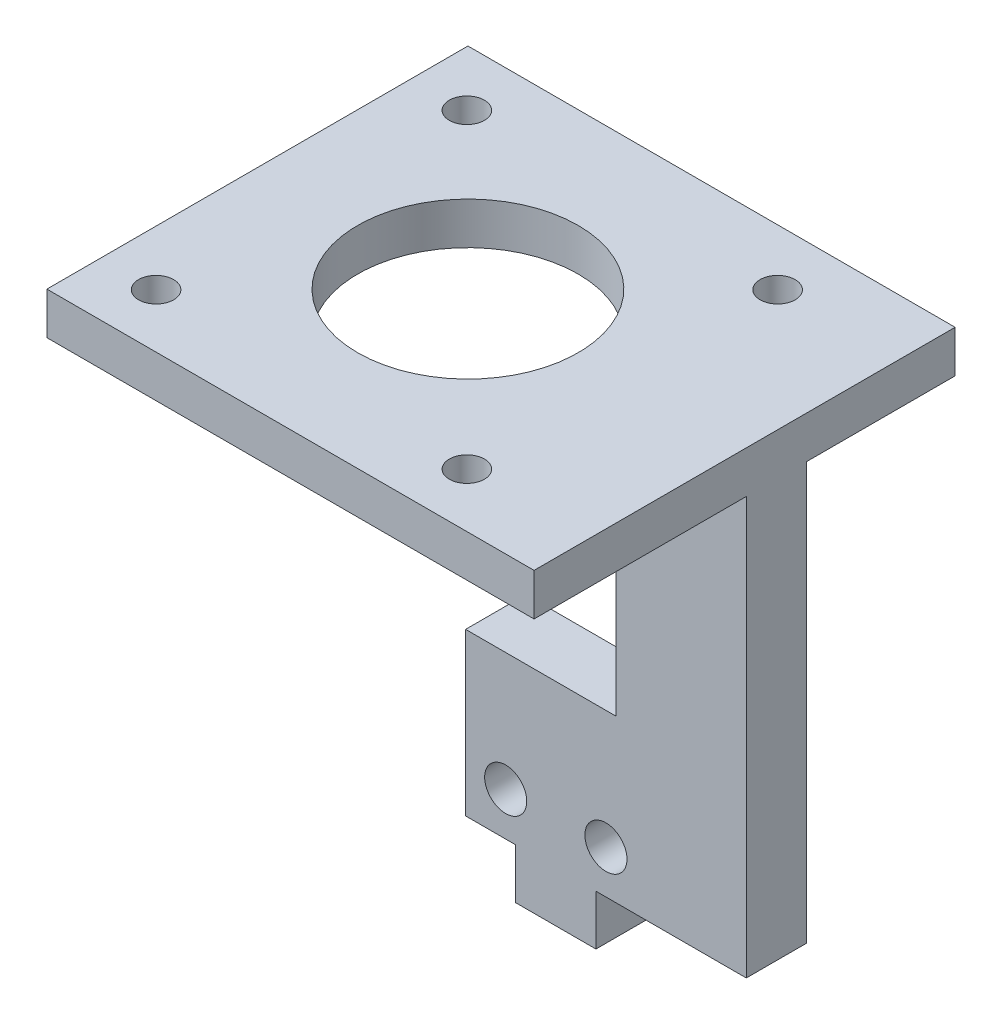
SolidWorks part; units mm, degrees
ref_plane "前视基准面" through (0, 0, 0) normal (0, 0, 1) x (1, 0, 0)
ref_plane "上视基准面" through (0, 0, 0) normal (0, 1, 0) x (1, 0, 0)
ref_plane "右视基准面" through (0, 0, 0) normal (1, 0, 0) x (0, 0, -1)
sketch "草图1" plane through (0, 0, 0) normal (0, 0, 1) x (1, 0, 0)
  line L1 (0, 0) -> (18, 0)
  line L2 (0, 0) -> (0, 50)
  line L3 (0, 50) -> (18, 50)
  line L4 (18, 0) -> (18, 50)
  dimension "D1" = 18
  dimension "D2" = 50
extrude "凸台-拉伸1" add sketch "草图1" along normal blind 6
sketch "草图3" plane through (0, 0, 6) normal (0, 0, 1) x (1, 0, 0)
  line L0 (9, 0) -> (9, 21.4804) construction
  line L1 (0, 0) -> (18, 0) construction
  circle A0 centre (4, 4.3045) radius 2.1
  circle A1 centre (14, 4.3045) radius 2.1
  dimension "D1" = 4.2
  dimension "D2" = 10
  dimension "D3" = 4.3045
extrude "切除-拉伸2" cut sketch "草图3" against normal blind 6
sketch "草图4" plane through (0, 0, 0) normal (0, -1, 0) x (1, 0, 0)
  line L0 (9, 6) -> (9, -13.3054) construction
  line L1 (0, 6) -> (18, 6) construction
  line L3 (13, 6) -> (5, 6)
  line L4 (13, 6) -> (13, -4)
  line L5 (13, -4) -> (5, -4)
  line L6 (5, 6) -> (5, -4)
  dimension "D1" = 8
  dimension "D2" = 10
extrude "凸台-拉伸2" add sketch "草图4" along normal blind 5
sketch "草图5" plane through (18, 0, 0) normal (1, 0, 0) x (0, 0, -1)
  line L0 (-6, 0) -> (-6, 50) construction
  line L1 (0, 0) -> (-6, 0)
  line L2 (0, 0) -> (0, 50)
  line L3 (0, 50) -> (-6, 50)
  line L4 (-6, 0) -> (-6, 50)
  line L5 (-6, 50) -> (0, 50) construction
  dimension "D1" = 0
extrude "凸台-拉伸3" add sketch "草图5" along normal blind 10
sketch "草图6" plane through (0, 0, 6) normal (0, 0, 1) x (1, 0, 0)
  line L0 (0, 50) -> (0, 0) construction
  line L1 (0, 16.1194) -> (15, 16.1194)
  line L2 (0, 16.1194) -> (0, 50)
  line L3 (0, 50) -> (15, 50)
  line L4 (15, 16.1194) -> (15, 50)
  line L5 (28, 50) -> (0, 50) construction
  dimension "D1" = 15
extrude "切除-拉伸3" cut sketch "草图6" against normal blind 10
sketch "草图7" plane through (0, 50, 0) normal (0, 1, 0) x (1, 0, 0)
  line L1 (28, -6) -> (9.8054, -6)
  line L2 (28, -6) -> (28, 2.4383)
  line L3 (28, 2.4383) -> (9.8054, 2.4383)
  line L4 (9.8054, -6) -> (9.8054, 2.4383)
extrude "切除-拉伸4" cut sketch "草图7" against normal blind 4.2
sketch "草图8" plane through (0, 45.8, 0) normal (0, 1, 0) x (1, 0, 0)
  line L0 (15, -6) -> (28, -6) construction
  line L1 (28, -27.17) -> (-30.5473, -27.17)
  line L2 (28, -27.17) -> (28, 14.83)
  line L3 (28, 14.83) -> (-30.5473, 14.83)
  line L4 (-30.5473, -27.17) -> (-30.5473, 14.83)
  line L5 (15, 0) -> (28, 0) construction
  dimension "D1" = 21.17
  dimension "D2" = 14.83
extrude "凸台-拉伸4" add sketch "草图8" against normal blind 4.2
sketch "草图9" plane through (-30.5473, 0, 0) normal (-1, 0, 0) x (0, 0, 1)
  line L1 (27.17, 45.8) -> (-22.0558, 45.8)
  line L2 (27.17, 45.8) -> (27.17, 39.7485)
  line L3 (27.17, 39.7485) -> (-22.0558, 39.7485)
  line L4 (-22.0558, 45.8) -> (-22.0558, 39.7485)
extrude "切除-拉伸5" cut sketch "草图9" against normal blind 9.95
sketch "草图15" plane through (0, 41.6, 0) normal (0, -1, 0) x (1, 0, 0)
  line L0 (0.4024, -12.4657) -> (0.4024, 23.6426) construction
  line L1 (0.4024, 6.2762) -> (-16.0251, 6.2762) construction
  line L2 (28, -14.83) -> (-20.5973, -14.83) construction
  line L3 (28, 0) -> (28, -14.83) construction
  circle A0 centre (15.9024, -9.2238) radius 1.75
  circle A1 centre (-15.0976, -9.2238) radius 1.75
  circle A2 centre (15.9024, 21.7762) radius 1.75
  circle A3 centre (-15.0976, 21.7762) radius 1.75
  dimension "D1" = 3.5
  dimension "D2" = 31
  dimension "D3" = 31
  dimension "D4" = 5.6062
  dimension "D5" = 12.0976
extrude "切除-拉伸6" cut sketch "草图15" against normal blind 9.95
sketch "草图16" plane through (0, 41.6, 0) normal (0, -1, 0) x (1, 0, 0)
  circle A0 centre (0.4, 6.17) radius 11
  dimension "D1" = 22
extrude "切除-拉伸7" cut sketch "草图16" against normal blind 10
